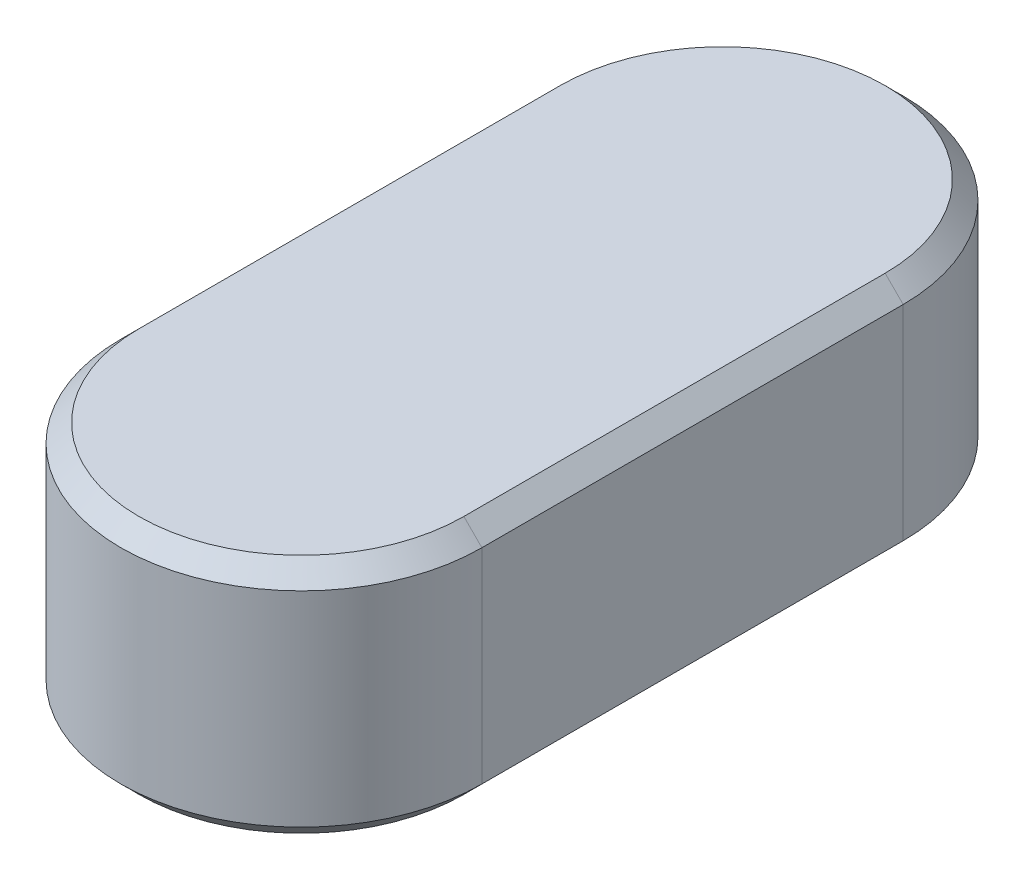
SolidWorks part; units mm, degrees
material "AISI 4340 Steel, normalized"
ref_plane "Front Plane" through (0, 0, 0) normal (0, 0, 1) x (1, 0, 0)
ref_plane "Top Plane" through (0, 0, 0) normal (0, 1, 0) x (1, 0, 0)
ref_plane "Right Plane" through (0, 0, 0) normal (1, 0, 0) x (0, 0, -1)
sketch "Sketch1" plane through (0, 0, 0) normal (0, 1, 0) x (1, 0, 0)
  line L0 (0, 0) -> (0, 14) construction
  line L1 (6, 0) -> (6, 14)
  line L2 (-6, 0) -> (-6, 14)
  arc A0 (6, 0) -> (-6, 0) centre (0, 0) cw
  arc A1 (6, 14) -> (-6, 14) centre (0, 14) ccw
  dimension "D1" = 14
  dimension "D2" = 6
  dimension "D3" = 6
extrude "Boss-Extrude1" add sketch "Sketch1" along normal blind 8
chamfer "Chamfer1" distance 0.6 8 edges at (-6, 8, -7) (0, 8, 6) (0, 8, -20) (6, 8, -7) (-6, 0, -7) (0, 0, 6) (0, 0, -20) (6, 0, -7)
